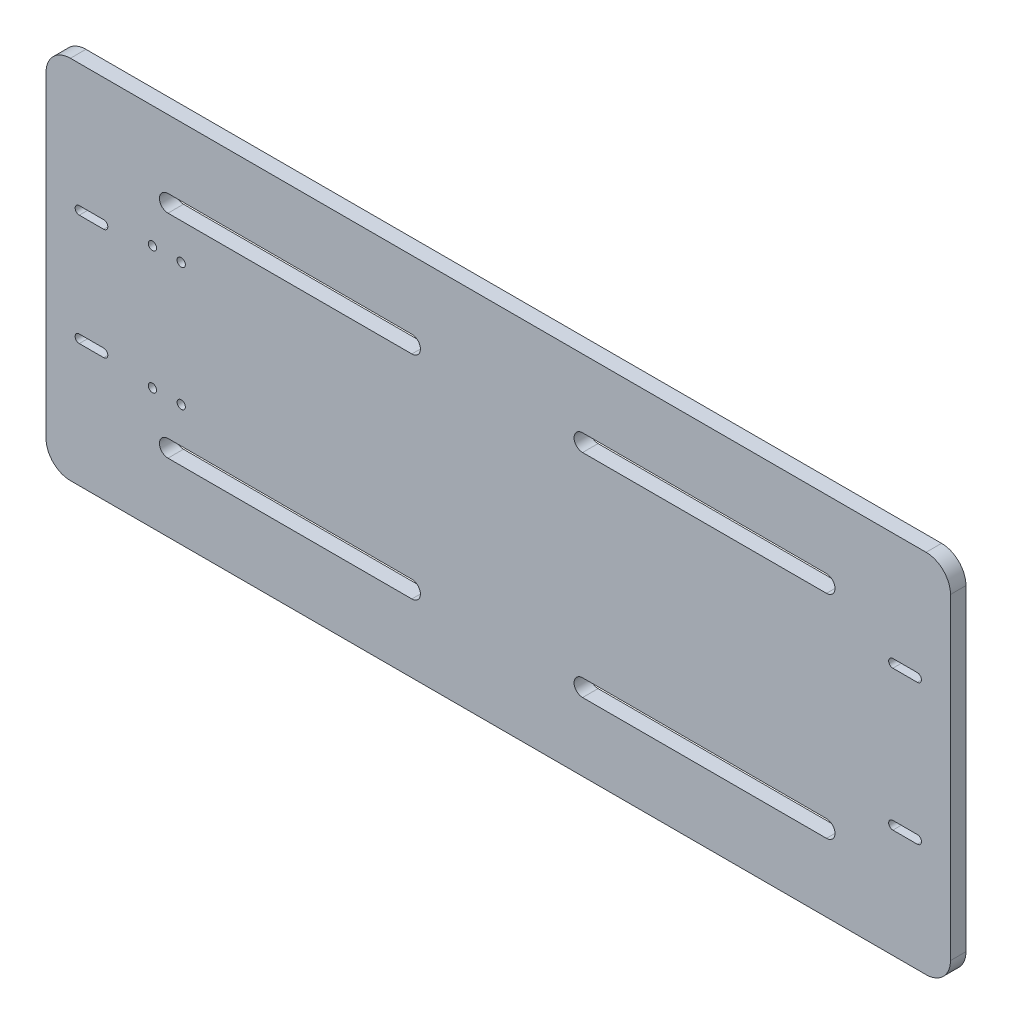
SolidWorks part; units mm, degrees
ref_plane "Front Plane" through (0, 0, 0) normal (0, 0, 1) x (1, 0, 0)
ref_plane "Top Plane" through (0, 0, 0) normal (0, 1, 0) x (1, 0, 0)
ref_plane "Right Plane" through (0, 0, 0) normal (1, 0, 0) x (0, 0, -1)
sketch "Sketch1" plane through (0, 0, 0) normal (0, 0, 1) x (1, 0, 0)
  line L1 (0, 0) -> (370.84, 0)
  line L2 (0, 0) -> (0, -150)
  line L3 (0, -150) -> (370.84, -150)
  line L4 (370.84, 0) -> (370.84, -150)
  dimension "D1" = 370.84
  dimension "D2" = 150
extrude "Boss-Extrude1" add sketch "Sketch1" along normal blind 6.35
fillet "Fillet3" radius 10 1 edges at (0, 0, 3.175)
fillet "Fillet4" radius 10 1 edges at (0, -150, 3.175)
fillet "Fillet5" radius 10 1 edges at (370.84, -150, 3.175)
fillet "Fillet6" radius 10 1 edges at (370.84, 0, 3.175)
sketch "Sketch3" plane through (0, 0, 6.35) normal (0, 0, 1) x (1, 0, 0)
  line L0 (10, -150) -> (360.84, -150) construction
  line L1 (360.84, 0) -> (10, 0) construction
  line L2 (185.42, 0) -> (185.42, -150) construction
  line L3 (0, -10) -> (0, -140) construction
  circle A0 centre (18.62, -52.205) radius 1.7
  circle A1 centre (18.62, -97.795) radius 1.7
  circle A2 centre (352.22, -103.75) radius 1.7
  circle A3 centre (352.22, -46.25) radius 1.7
  dimension "D1" = 3.4
  dimension "D2" = 3.4
  dimension "D3" = 45.59
  dimension "D4" = 52.205
  dimension "D7" = 57.5
  dimension "D9" = 3.4
  dimension "D10" = 3.4
  dimension "D11" = 333.6
  dimension "D5" = 18.62
  dimension "D6" = 18.62
  dimension "D8" = 46.25
extrude "Cut-Extrude1" cut sketch "Sketch3" against normal blind 10
sketch "Sketch4" plane through (0, 0, 6.35) normal (0, 0, 1) x (1, 0, 0)
  line L0 (50, -31.5) -> (150, -31.5) construction
  line L1 (50, -28) -> (150, -28)
  line L2 (50, -35) -> (150, -35)
  line L3 (220, -31.5) -> (320, -31.5) construction
  line L4 (220, -28) -> (320, -28)
  line L5 (220, -35) -> (320, -35)
  line L6 (50, -118.5) -> (150, -118.5) construction
  line L7 (50, -115) -> (150, -115)
  line L8 (50, -122) -> (150, -122)
  line L9 (220, -118.5) -> (320, -118.5) construction
  line L10 (220, -115) -> (320, -115)
  line L11 (220, -122) -> (320, -122)
  line L14 (360.84, 0) -> (10, 0) construction
  line L16 (0, -10) -> (0, -140) construction
  arc A0 (50, -28) -> (50, -35) centre (50, -31.5) ccw
  arc A1 (150, -35) -> (150, -28) centre (150, -31.5) ccw
  arc A2 (220, -28) -> (220, -35) centre (220, -31.5) ccw
  arc A3 (320, -35) -> (320, -28) centre (320, -31.5) ccw
  arc A4 (50, -115) -> (50, -122) centre (50, -118.5) ccw
  arc A5 (150, -122) -> (150, -115) centre (150, -118.5) ccw
  arc A6 (220, -115) -> (220, -122) centre (220, -118.5) ccw
  arc A7 (320, -122) -> (320, -115) centre (320, -118.5) ccw
  point P2 (100, -31.5)
  point P7 (270, -31.5)
  point P14 (100, -118.5)
  point P21 (270, -118.5)
  dimension "D1" = 7
  dimension "D2" = 7
  dimension "D3" = 7
  dimension "D4" = 7
  dimension "D5" = 80
  dimension "D6" = 28
  dimension "D7" = 100
  dimension "D8" = 100
  dimension "D9" = 100
  dimension "D10" = 100
  dimension "D11" = 70
  dimension "D12" = 50
  dimension "D13" = 50
  dimension "D14" = 70
extrude "Cut-Extrude2" cut sketch "Sketch4" against normal blind 10
sketch "Sketch6" plane through (0, 0, 6.35) normal (0, 0, 1) x (1, 0, 0)
  line L0 (13.62, -52.205) -> (23.62, -52.205) construction
  line L1 (13.62, -50.505) -> (23.62, -50.505)
  line L2 (13.62, -53.905) -> (23.62, -53.905)
  line L3 (13.62, -97.795) -> (23.62, -97.795) construction
  line L4 (13.62, -96.095) -> (23.62, -96.095)
  line L5 (13.62, -99.495) -> (23.62, -99.495)
  line L6 (347.22, -46.25) -> (357.22, -46.25) construction
  line L7 (347.22, -44.525) -> (357.22, -44.525)
  line L8 (347.22, -47.975) -> (357.22, -47.975)
  line L9 (347.22, -103.75) -> (357.22, -103.75) construction
  line L10 (347.22, -102.025) -> (357.22, -102.025)
  line L11 (347.22, -105.475) -> (357.22, -105.475)
  line L13 (360.84, 0) -> (10, 0) construction
  arc A0 (13.62, -50.505) -> (13.62, -53.905) centre (13.62, -52.205) ccw
  arc A1 (23.62, -53.905) -> (23.62, -50.505) centre (23.62, -52.205) ccw
  arc A2 (13.62, -96.095) -> (13.62, -99.495) centre (13.62, -97.795) ccw
  arc A3 (23.62, -99.495) -> (23.62, -96.095) centre (23.62, -97.795) ccw
  arc A4 (347.22, -44.525) -> (347.22, -47.975) centre (347.22, -46.25) ccw
  arc A5 (357.22, -47.975) -> (357.22, -44.525) centre (357.22, -46.25) ccw
  arc A6 (347.22, -102.025) -> (347.22, -105.475) centre (347.22, -103.75) ccw
  arc A7 (357.22, -105.475) -> (357.22, -102.025) centre (357.22, -103.75) ccw
  circle A8 centre (43.62, -49.75) radius 1.7
  circle A9 centre (43.62, -100.25) radius 1.7
  circle A10 centre (55.42, -49.75) radius 1.7
  circle A11 centre (55.42, -100.25) radius 1.7
  point P2 (18.62, -52.205)
  point P9 (18.62, -97.795)
  point P18 (352.22, -46.25)
  point P26 (352.22, -103.75)
  dimension "D2" = 10
  dimension "D3" = 10
  dimension "D6" = 10
  dimension "D8" = 10
  dimension "D9" = 3.4
  dimension "D10" = 3.4
  dimension "D11" = 20
  dimension "D12" = 20
  dimension "D13" = 50.5
  dimension "D14" = 49.75
  dimension "D15" = 3.4
  dimension "D16" = 3.4
  dimension "D17" = 11.8
  dimension "D18" = 11.8
  dimension "D1" = 3.4
  dimension "D4" = 3.4
  dimension "D5" = 3.45
  dimension "D7" = 3.45
extrude "Cut-Extrude3" cut sketch "Sketch6" against normal through all
